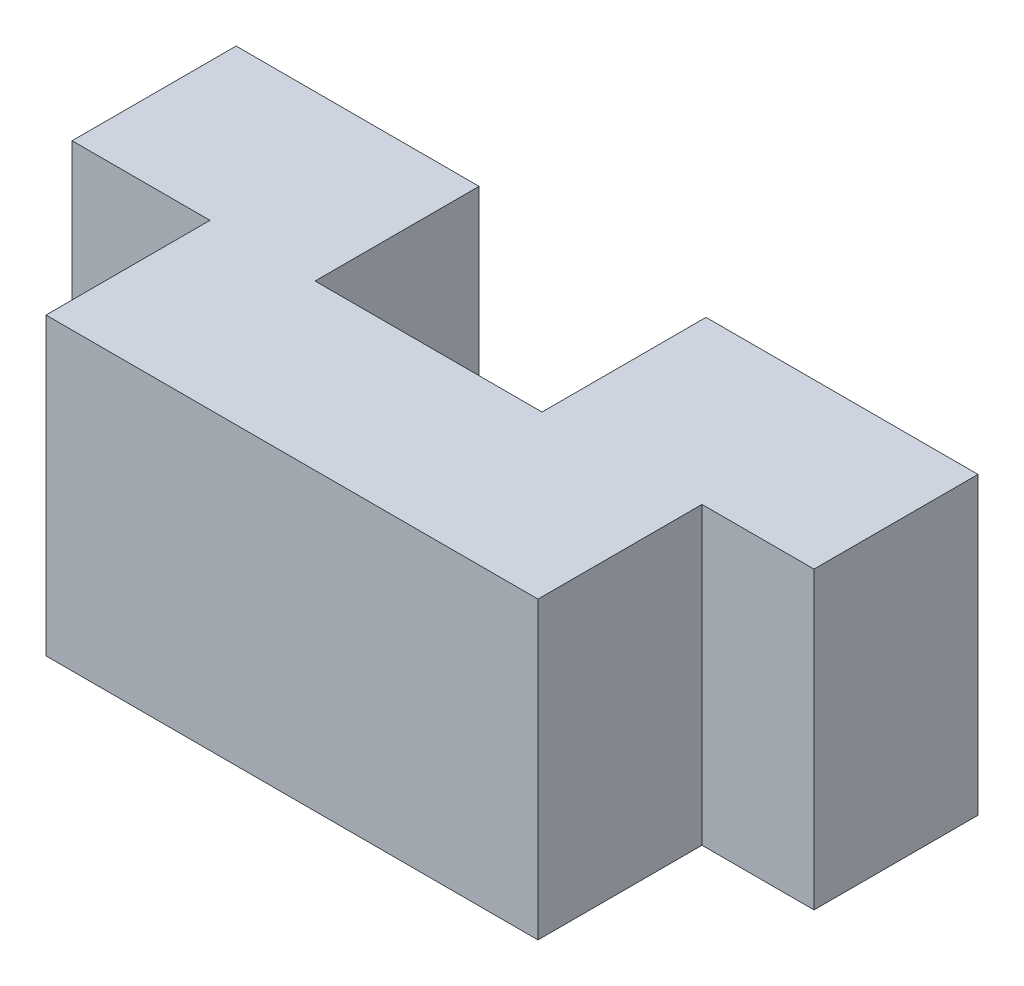
SolidWorks part; units mm, degrees
ref_plane "Front Plane" through (0, 0, 0) normal (0, 0, 1) x (1, 0, 0)
ref_plane "Top Plane" through (0, 0, 0) normal (0, 1, 0) x (1, 0, 0)
ref_plane "Right Plane" through (0, 0, 0) normal (1, 0, 0) x (0, 0, -1)
sketch "Sketch1" plane through (0, 0, 0) normal (0, 0, 1) x (1, 0, 0)
  line L0 (7.5, 4.5) -> (-7.5, 4.5)
  line L1 (-7.5, 4.5) -> (-7.5, -4.5)
  line L2 (-7.5, -4.5) -> (7.5, -4.5)
  line L3 (7.5, -4.5) -> (7.5, 4.5)
  point P2 (0, 4.5)
  point P5 (-7.5, 0)
  dimension "D1" = 15
  dimension "D2" = 9
extrude "Boss-Extrude1" add sketch "Sketch1" along normal blind 5
sketch "Sketch2" plane through (0, 0, 0) normal (0, 0, 1) x (1, 0, 0)
  line L0 (7.5, 4.5) -> (-7.5, 4.5) construction
  line L1 (-4.2964, 4.5) -> (-11.7046, 4.5)
  line L2 (-4.2964, 4.5) -> (-4.2964, -4.5)
  line L3 (-4.2964, -4.5) -> (-11.7046, -4.5)
  line L4 (-11.7046, 4.5) -> (-11.7046, -4.5)
  line L5 (-7.5, -4.5) -> (7.5, -4.5) construction
  line L6 (2.6221, 4.5) -> (10.9148, 4.5)
  line L7 (2.6221, 4.5) -> (2.6221, -4.5)
  line L8 (2.6221, -4.5) -> (10.9148, -4.5)
  line L9 (10.9148, 4.5) -> (10.9148, -4.5)
extrude "Boss-Extrude2" add sketch "Sketch2" against normal blind 5
